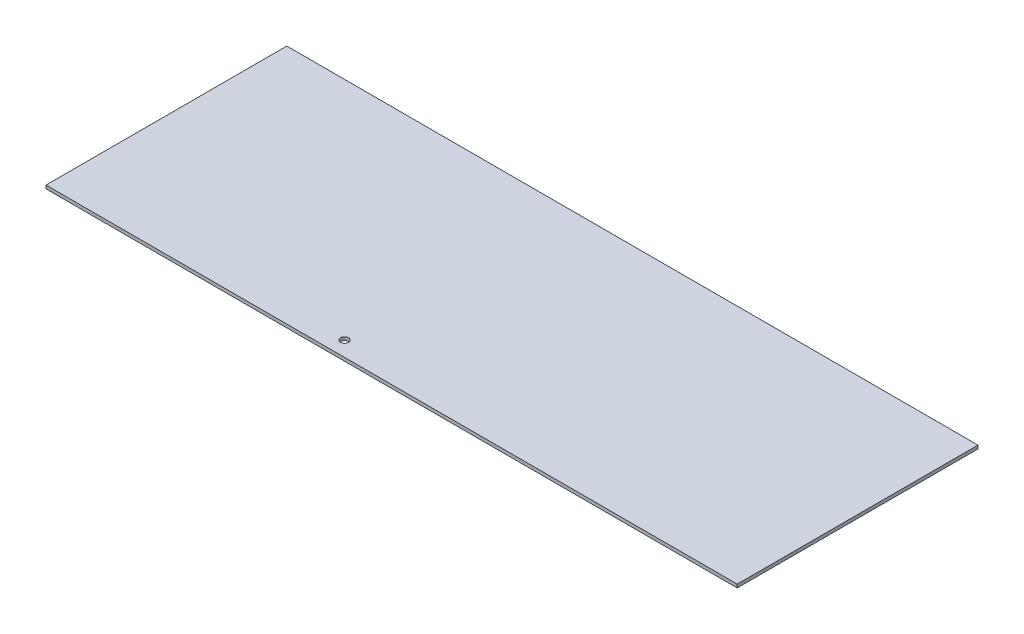
SolidWorks part; units mm, degrees
material "Copper"
ref_plane "Front Plane" through (0, 0, 0) normal (0, 0, 1) x (1, 0, 0)
ref_plane "Top Plane" through (0, 0, 0) normal (0, 1, 0) x (1, 0, 0)
ref_plane "Right Plane" through (0, 0, 0) normal (1, 0, 0) x (0, 0, -1)
sketch "Sketch1" plane through (0, 0, 0) normal (0, 1, 0) x (1, 0, 0)
  line L1 (0, 0) -> (344.4875, 0)
  line L2 (0, 0) -> (0, 120)
  line L3 (0, 120) -> (344.4875, 120)
  line L4 (344.4875, 0) -> (344.4875, 120)
  circle A0 centre (141.2875, 7.5) radius 2
  point P5 (141.2875, 7.5)
extrude "Boss-Extrude1" add sketch "Sketch1" along normal blind 1.65
